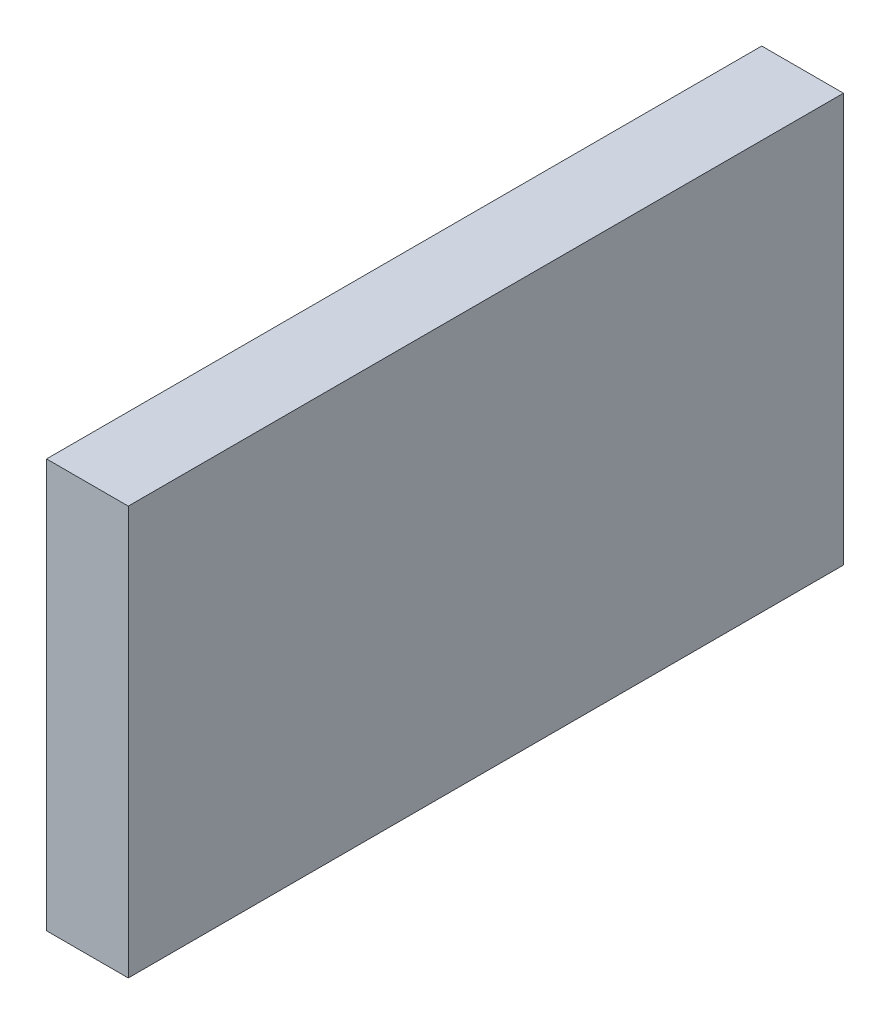
SolidWorks part; units mm, degrees
ref_plane "Front Plane" through (0, 0, 0) normal (0, 0, 1) x (1, 0, 0)
ref_plane "Top Plane" through (0, 0, 0) normal (0, 1, 0) x (1, 0, 0)
ref_plane "Right Plane" through (0, 0, 0) normal (1, 0, 0) x (0, 0, -1)
sketch "Sketch2" plane through (0, 0, 0) normal (1, 0, 0) x (0, 0, -1)
  line L0 (0, 0) -> (0, 20)
  line L1 (0, 20) -> (35, 20)
  line L2 (35, 20) -> (35, 0)
  line L3 (35, 0) -> (0, 0)
  dimension "D1" = 35
  dimension "D2" = 20
extrude "Boss-Extrude1" add sketch "Sketch2" along normal blind 4 contours L3 L0 L1 L2
